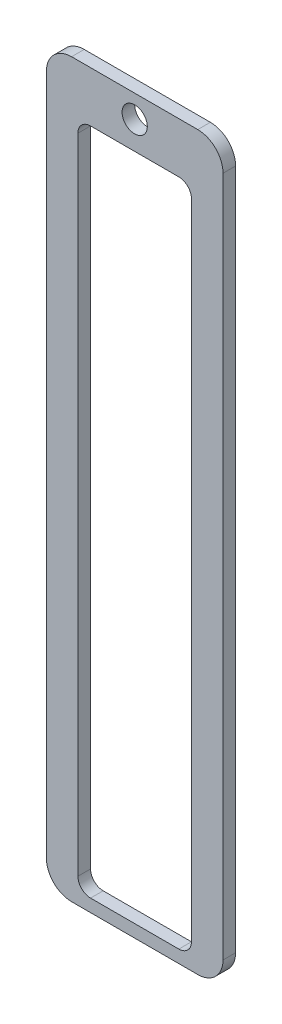
SolidWorks part; units mm, degrees
ref_plane "Front Plane" through (0, 0, 0) normal (0, 0, 1) x (1, 0, 0)
ref_plane "Top Plane" through (0, 0, 0) normal (0, 1, 0) x (1, 0, 0)
ref_plane "Right Plane" through (0, 0, 0) normal (1, 0, 0) x (0, 0, -1)
sketch "Sketch4" plane through (0, 0, 0) normal (0, 0, 1) x (1, 0, 0)
  line L1 (-25, -290) -> (25, -290)
  line L2 (-35, -280) -> (-35, -10)
  line L3 (-25, 0) -> (25, 0)
  line L4 (35, -280) -> (35, -10)
  line L5 (-35, -290) -> (35, 0) construction
  line L6 (-35, 0) -> (35, -290) construction
  arc A0 (25, -290) -> (35, -280) centre (25, -280) ccw
  arc A1 (-25, -290) -> (-35, -280) centre (-25, -280) cw
  arc A2 (25, 0) -> (35, -10) centre (25, -10) cw
  arc A3 (-35, -10) -> (-25, 0) centre (-25, -10) cw
  point P0 (0, -145)
  dimension "D3" = 10
  dimension "D1" = 290
  dimension "D2" = 70
extrude "Boss-Extrude3" add sketch "Sketch4" along normal blind 5
sketch "Sketch6" plane through (0, 0, 5) normal (0, 0, 1) x (1, 0, 0)
  line L0 (-35, -10) -> (-35, -280) construction
  line L1 (-17.5, -20) -> (17.5, -20)
  line L2 (-22.5, -25) -> (-22.5, -280)
  line L3 (-17.5, -285) -> (17.5, -285)
  line L4 (22.5, -25) -> (22.5, -280)
  line L6 (25, 0) -> (-25, 0) construction
  circle A0 centre (0, -9) radius 5
  arc A1 (17.5, -285) -> (22.5, -280) centre (17.5, -280) ccw
  arc A2 (-22.5, -280) -> (-17.5, -285) centre (-17.5, -280) ccw
  arc A3 (17.5, -20) -> (22.5, -25) centre (17.5, -25) cw
  arc A4 (-17.5, -20) -> (-22.5, -25) centre (-17.5, -25) ccw
  point P14 (22.5, -285)
  point P19 (22.5, -20)
  point P22 (-22.5, -20)
  dimension "D5" = 10
  dimension "D8" = 5
  dimension "D1" = 265
  dimension "D2" = 45
  dimension "D3" = 12.5
  dimension "D4" = 20
  dimension "D6" = 9
extrude "Cut-Extrude1" cut sketch "Sketch6" against normal through all
